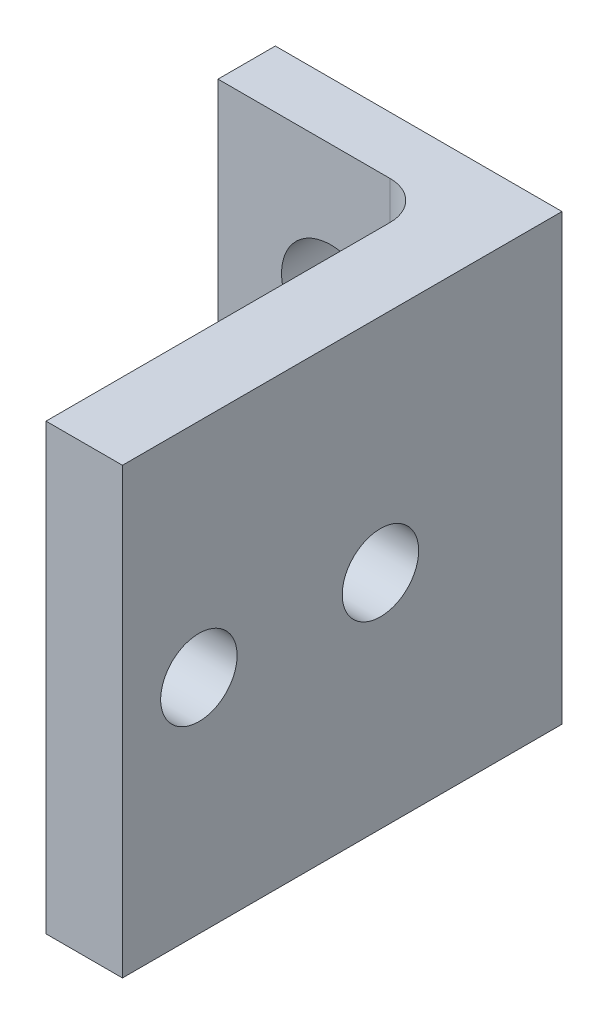
SolidWorks part; units mm, degrees
ref_plane "Front Plane" through (0, 0, 0) normal (0, 0, 1) x (1, 0, 0)
ref_plane "Top Plane" through (0, 0, 0) normal (0, 1, 0) x (1, 0, 0)
ref_plane "Right Plane" through (0, 0, 0) normal (1, 0, 0) x (0, 0, -1)
sketch "Sketch1" plane through (0, 0, 0) normal (0, 0, 1) x (1, 0, 0)
  line L1 (50.33, 18.6565) -> (65.33, 18.6565)
  line L2 (50.33, 18.6565) -> (50.33, -4.58)
  line L3 (50.33, -4.58) -> (65.33, -4.58)
  line L4 (65.33, 18.6565) -> (65.33, -4.58)
  circle A0 centre (56.235, 11.52) radius 2.58
  dimension "D1" = 23.2365
  dimension "D2" = 15
extrude "Boss-Extrude1" add sketch "Sketch1" along normal blind 3
sketch "Sketch2" plane through (0, 0, 3) normal (0, 0, 1) x (1, 0, 0)
  line L0 (65.33, 18.6565) -> (50.33, 18.6565) construction
  line L1 (65.33, -4.58) -> (61.33, -4.58)
  line L2 (65.33, -4.58) -> (65.33, 18.6565)
  line L3 (65.33, 18.6565) -> (61.33, 18.6565)
  line L4 (61.33, -4.58) -> (61.33, 18.6565)
  dimension "D1" = 4
extrude "Boss-Extrude2" add sketch "Sketch2" along normal blind 20
sketch "Sketch3" plane through (65.33, 0, 0) normal (1, 0, 0) x (0, 0, -1)
  line L0 (-23, -4.58) -> (-23, 18.6565) construction
  line L1 (-19, 18.6565) -> (-19, 7.0383) construction
  line L2 (-23, 18.6565) -> (0, 18.6565) construction
  line L3 (-19, 7.0383) -> (-19, -4.58) construction
  line L4 (-23, -4.58) -> (0, -4.58) construction
  circle A0 centre (-19, 7.0383) radius 2
  circle A1 centre (-9.5, 7.0383) radius 2
  dimension "D1" = 4
  dimension "D2" = 4
  dimension "D3" = 9.5
  dimension "D4" = 4
extrude "Cut-Extrude1" cut sketch "Sketch3" against normal blind 4
fillet "Fillet1" radius 2 1 edges at (61.33, 7.0383, 3)
sketch "Sketch4" plane through (0, 0, 3) normal (0, 0, 1) x (1, 0, 0)
  circle A0 centre (56.235, 11.52) radius 4.75
  dimension "D1" = 9.5
extrude "Cut-Extrude2" cut sketch "Sketch4" along normal blind 4
